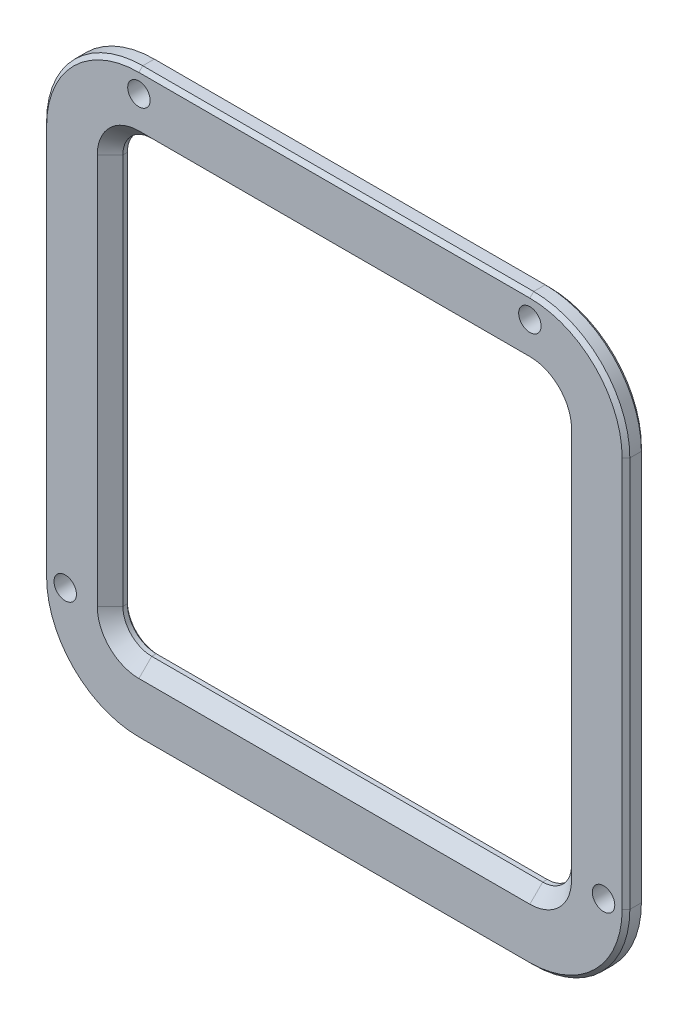
SolidWorks part; units mm, degrees
ref_plane "Front Plane" through (0, 0, 0) normal (0, 0, 1) x (1, 0, 0)
ref_plane "Top Plane" through (0, 0, 0) normal (0, 1, 0) x (1, 0, 0)
ref_plane "Right Plane" through (0, 0, 0) normal (1, 0, 0) x (0, 0, -1)
sketch "Sketch2" plane through (0, 0, 0) normal (0, 0, 1) x (1, 0, 0)
  line L4 (-44.2196, -34.3373) -> (-44.2196, 26.6627)
  line L5 (-29.2196, 41.6627) -> (31.7804, 41.6627)
  line L6 (46.7804, 26.6627) -> (46.7804, -34.3373)
  line L7 (31.7804, -49.3373) -> (-29.2196, -49.3373)
  line L8 (-29.2196, 31.1627) -> (31.7804, 31.1627)
  line L9 (36.2804, 26.6627) -> (36.2804, -34.3373)
  line L10 (31.7804, -38.8373) -> (-29.2196, -38.8373)
  line L11 (-33.7196, -34.3373) -> (-33.7196, 26.6627)
  circle A7 centre (43.2804, -34.3373) radius 1.25
  circle A8 centre (31.7804, 38.1627) radius 1.25
  circle A9 centre (-29.2196, 38.1627) radius 1.25
  circle A10 centre (-40.7196, -34.3373) radius 1.25
  arc A11 (-29.2196, 41.6627) -> (-44.2196, 26.6627) centre (-29.2196, 26.6627) ccw
  arc A12 (46.7804, 26.6627) -> (31.7804, 41.6627) centre (31.7804, 26.6627) ccw
  arc A13 (31.7804, -49.3373) -> (46.7804, -34.3373) centre (31.7804, -34.3373) ccw
  arc A15 (-44.2196, -34.3373) -> (-29.2196, -49.3373) centre (-29.2196, -34.3373) ccw
  arc A16 (36.2804, 26.6627) -> (31.7804, 31.1627) centre (31.7804, 26.6627) ccw
  arc A17 (31.7804, -38.8373) -> (36.2804, -34.3373) centre (31.7804, -34.3373) ccw
  arc A18 (-33.7196, -34.3373) -> (-29.2196, -38.8373) centre (-29.2196, -34.3373) ccw
  arc A19 (-29.2196, 31.1627) -> (-33.7196, 26.6627) centre (-29.2196, 26.6627) ccw
  dimension "D1" = 10.5
extrude "Boss-Extrude1" add sketch "Sketch2" along normal blind 3 contours L4 A15 L7 A13 L6 A12 L5 A11 A19 L8 A16 L9 A17 L10 A18 L11 A7 A8 A9 A10
chamfer "Chamfer1" distance 2 angle 45 8 edges at (1.2804, -38.8373, 3) (-32.4016, -37.5192, 3) (34.9624, -37.5192, 3) (-33.7196, -3.8373, 3) (36.2804, -3.8373, 3) (-32.4016, 29.8447, 3) (34.9624, 29.8447, 3) (1.2804, 31.1627, 3)
chamfer "Chamfer2" distance 0.6 angle 45 16 edges at (-39.8262, -44.9439, 0) (1.2804, -49.3373, 0) (-44.2196, -3.8373, 0) (42.387, -44.9439, 0) (-39.8262, 37.2693, 0) (46.7804, -3.8373, 0) (1.2804, 41.6627, 0) (42.387, 37.2693, 0) (1.2804, -49.3373, 3) (-39.8262, -44.9439, 3) (42.387, -44.9439, 3) (-44.2196, -3.8373, 3) (46.7804, -3.8373, 3) (-39.8262, 37.2693, 3) (42.387, 37.2693, 3) (1.2804, 41.6627, 3)
chamfer "Chamfer3" distance 0.3 angle 45 8 edges at (1.2804, -38.8373, 0) (-32.4016, -37.5192, 0) (34.9624, -37.5192, 0) (-33.7196, -3.8373, 0) (36.2804, -3.8373, 0) (-32.4016, 29.8447, 0) (34.9624, 29.8447, 0) (1.2804, 31.1627, 0)
sketch "Sketch3" plane through (0, 0, 3) normal (0, 0, 1) x (1, 0, 0)
  circle A8 centre (-29.2196, 38.1627) radius 1.75
  circle A9 centre (-29.2196, 38.1627) radius 1.75
  circle A11 centre (31.7804, 38.1627) radius 1.75
  circle A12 centre (31.7804, 38.1627) radius 1.75
  circle A14 centre (-40.7196, -34.3373) radius 1.75
  circle A15 centre (-40.7196, -34.3373) radius 1.75
  circle A17 centre (43.2804, -34.3373) radius 1.75
  circle A18 centre (43.2804, -34.3373) radius 1.75
  dimension "D1" = 0.5
  dimension "D2" = 0.5
  dimension "D3" = 0.5
  dimension "D4" = 0.5
extrude "Cut-Extrude1" cut sketch "Sketch3" against normal through all
